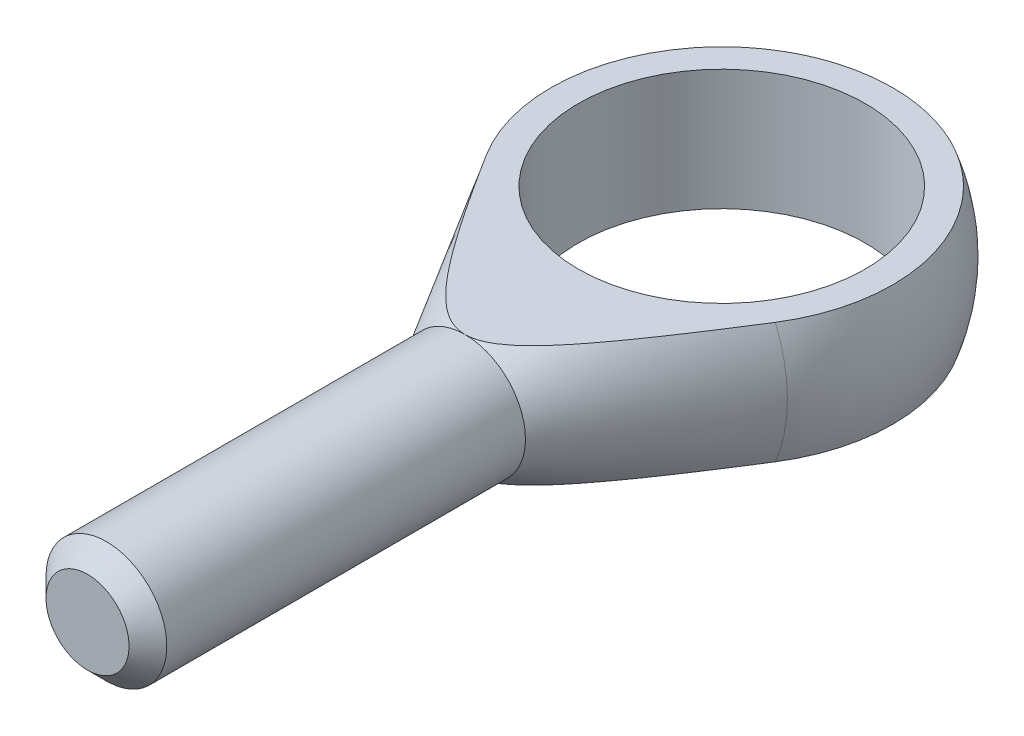
SolidWorks part; units mm, degrees
material "1.0545 (S355N)"
ref_plane "Płaszczyzna przednia" through (0, 0, 0) normal (0, 0, 1) x (1, 0, 0)
ref_plane "Płaszczyzna górna" through (0, 0, 0) normal (0, 1, 0) x (1, 0, 0)
ref_plane "Płaszczyzna prawa" through (0, 0, 0) normal (1, 0, 0) x (0, 0, -1)
sketch "Szkic1" plane through (0, 0, 0) normal (0, 1, 0) x (1, 0, 0)
  line L0 (0, 26.0435) -> (0, -71.4286) construction
  line L1 (-4, -42) -> (4, -42)
  line L2 (4, -42) -> (4, -17)
  line L3 (-4, -42) -> (-4, -17)
  line L4 (-10.3753, -6.0293) -> (-4, -17)
  line L5 (4, -17) -> (10.3753, -6.0293)
  line L6 (-4, -17) -> (4, -17)
  line L7 (0, 12) -> (0, -42)
  arc A0 (10.3753, -6.0293) -> (-10.3753, -6.0293) centre (0, 0) ccw
  point P7 (0, -42)
  dimension "d4" = 24
  dimension "d2" = 8
  dimension "l1" = 42
  dimension "l3" = 25
revolve "Obrót1" add sketch "Szkic1" angle 360 about L0
sketch "Szkic2" plane through (0, 0, 0) normal (1, 0, 0) x (0, 0, -1)
  line L4 (-17, 4) -> (11.3137, 4)
  line L5 (-17, -4) -> (11.3137, -4)
  line L6 (-17, -4) -> (-6.0293, -10.3753) construction
  line L7 (-6.0293, 10.3753) -> (-17, 4) construction
  line L8 (-17, -4) -> (-6.0293, -10.3753)
  line L9 (-6.0293, 10.3753) -> (-17, 4)
  arc A0 (-6.0293, -10.3753) -> (-6.0293, 10.3753) centre (0, 0) ccw construction
  arc A1 (-6.0293, -10.3753) -> (11.3137, -4) centre (0, 0) ccw
  arc A2 (11.3137, 4) -> (-6.0293, 10.3753) centre (0, 0) ccw
extrude "Wytnij-wyciągnięcie1" cut sketch "Szkic2" against normal through all both and the other way through all
sketch "Szkic3" plane through (0, 0, 0) normal (0, 1, 0) x (1, 0, 0)
  circle A0 centre (0, 0) radius 9.5
  dimension "b" = 19
extrude "Wytnij-wyciągnięcie2" cut sketch "Szkic3" against normal through all both and the other way through all contours A0
chamfer "Sfazowanie1" distance 1.25 angle 45 1 edges at (-4, 0, 42)
equation "\"D1@Sfazowanie1\"=\"l3@Szkic1\"*0.05"
